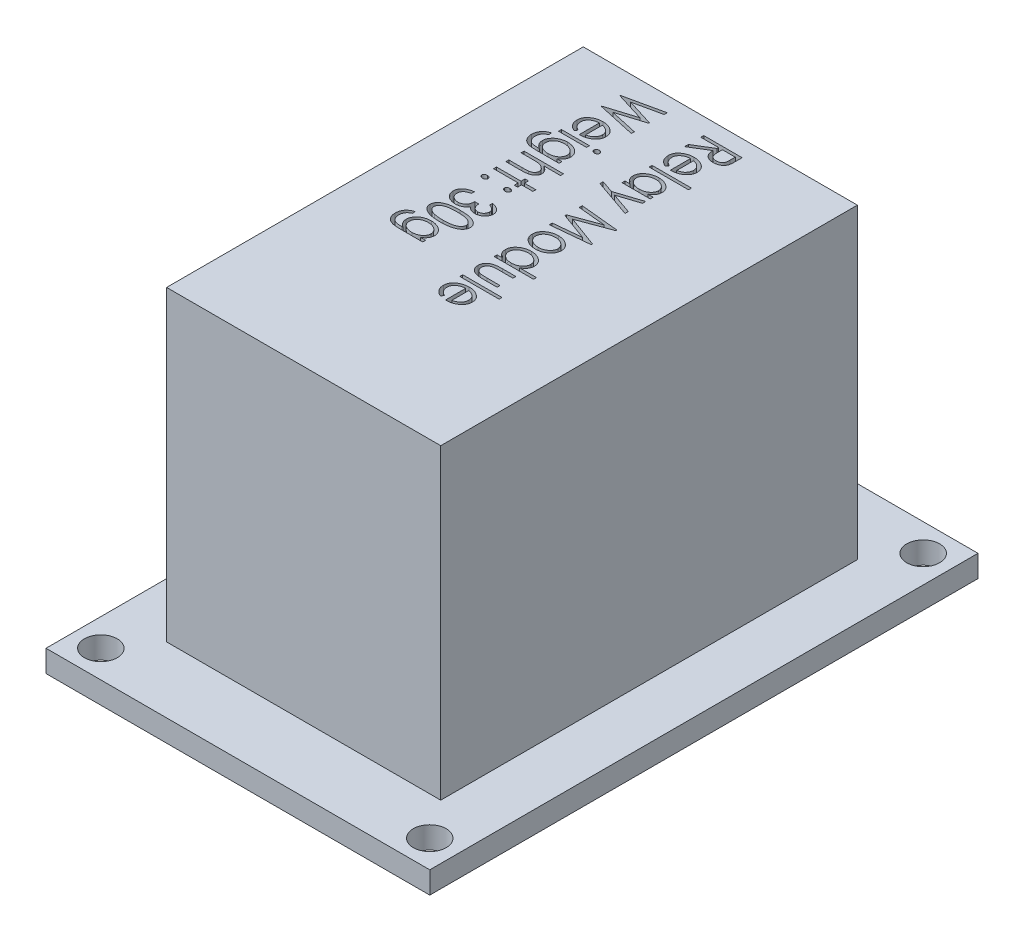
SolidWorks part; units mm, degrees
ref_plane "Front Plane" through (0, 0, 0) normal (0, 0, 1) x (1, 0, 0)
ref_plane "Top Plane" through (0, 0, 0) normal (0, 1, 0) x (1, 0, 0)
ref_plane "Right Plane" through (0, 0, 0) normal (1, 0, 0) x (0, 0, -1)
sketch "Sketch1" plane through (0, 0, 0) normal (0, 1, 0) x (1, 0, 0)
  line L0 (-17.5, -25) -> (17.5, -25)
  line L1 (-17.5, -25) -> (-17.5, 25)
  line L2 (-17.5, 25) -> (17.5, 25)
  line L3 (17.5, -25) -> (17.5, 25)
  line L4 (-17.5, -25) -> (17.5, 25) construction
  line L5 (-17.5, 25) -> (17.5, -25) construction
  circle A0 centre (-15, -22.5) radius 1.5
  circle A1 centre (15, -22.5) radius 1.5
  circle A2 centre (15, 22.5) radius 1.5
  circle A3 centre (-15, 22.5) radius 1.5
  point P4 (0, 0)
  dimension "D4" = 3
  dimension "D6" = 3
  dimension "D11" = 3
  dimension "D14" = 3
  dimension "D1" = 35
  dimension "D2" = 50
  dimension "D3" = 2.5
  dimension "D5" = 2.5
  dimension "D7" = 2.5
  dimension "D8" = 2.5
  dimension "D9" = 2.5
  dimension "D10" = 2.5
  dimension "D12" = 2.5
  dimension "D13" = 2.5
extrude "Boss-Extrude1" add sketch "Sketch1" along normal blind 2
sketch "Sketch2" plane through (0, 2, 0) normal (0, 1, 0) x (1, 0, 0)
  line L0 (-17.5, 25) -> (-17.5, -25) construction
  line L1 (-12.5, -19) -> (12.5, -19)
  line L2 (-12.5, -19) -> (-12.5, 19)
  line L3 (-12.5, 19) -> (12.5, 19)
  line L4 (12.5, -19) -> (12.5, 19)
  line L5 (-12.5, -19) -> (12.5, 19) construction
  line L6 (-12.5, 19) -> (12.5, -19) construction
  line L7 (-17.5, -25) -> (17.5, -25) construction
  point P0 (0, 0)
  dimension "D1" = 5
  dimension "D2" = 6
extrude "Boss-Extrude2" add sketch "Sketch2" along normal blind 28
sketch "Sketch3" plane through (0, 30, 0) normal (0, 1, 0) x (1, 0, 0)
  line L0 (0, 17.8034) -> (0, -13.093) construction
  text T0 "Relay Module\r\nWeight: 30g" font "Century Gothic" height 3.5
  dimension "D1" = 15.4464
  dimension "D2" = 15.45
  dimension "D3" = 30.8964
extrude "Cut-Extrude1" cut sketch "Sketch3" against normal blind 2
